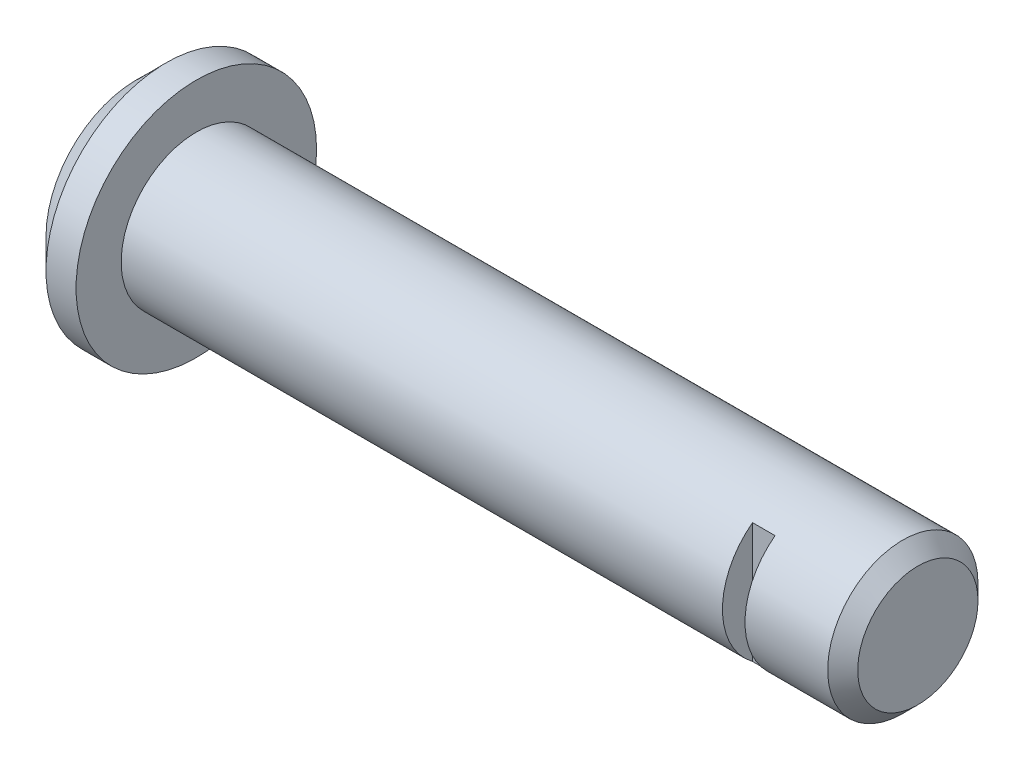
SolidWorks part; units mm, degrees
ref_plane "Front Plane" through (0, 0, 0) normal (0, 0, 1) x (1, 0, 0)
ref_plane "Top Plane" through (0, 0, 0) normal (0, 1, 0) x (1, 0, 0)
ref_plane "Right Plane" through (0, 0, 0) normal (1, 0, 0) x (0, 0, -1)
sketch "Sketch1" plane through (0, 0, 0) normal (0, 1, 0) x (1, 0, 0)
  line L0 (0, 0) -> (94, 0)
  line L1 (96, 2) -> (96, 10)
  line L2 (67.8773, 10) -> (-69.8369, 10) construction
  line L3 (0, 0) -> (0, -6)
  line L4 (0, -6) -> (-4, -6)
  line L5 (-8, -2) -> (-8, 10)
  line L6 (94, 0) -> (96, 2)
  line L7 (-4, -6) -> (-8, -2)
  line L8 (96, 10) -> (-8, 10)
  point P1 (96, 0)
  point P8 (-8, -6)
  dimension "D1" = 2
  dimension "D2" = 45
  dimension "D3" = 4
  dimension "D4" = 45
  dimension "D5" = 16
  dimension "D6" = 104
  dimension "D7" = 10
  dimension "D8" = 8
revolve "Revolve1" add sketch "Sketch1" angle 360 about L2
ref_plane "Plane1" through (0, 40, 0) normal (0, 1, 0) x (1, 0, 0)
sketch "Sketch2" plane through (0, 40, 0) normal (0, 1, 0) x (1, 0, 0)
  line L0 (0, 0) -> (94, 0) construction
  line L1 (94, 20) -> (0, 20) construction
  line L2 (0, 0) -> (94, 0) construction
  line L3 (94, 20) -> (0, 20) construction
  line L4 (0, 20) -> (0, 0) construction
  line L5 (94, 20) -> (94, 0) construction
  line L6 (80, 0) -> (80, 4)
  line L7 (80, 4) -> (83, 4)
  line L8 (83, 4) -> (83, 0)
  dimension "D1" = 4
  dimension "D2" = 11
  dimension "D3" = 3
extrude "Cut-Extrude2" cut sketch "Sketch2" against normal through all and the other way through all flip side to cut contours L6 L7 L8
